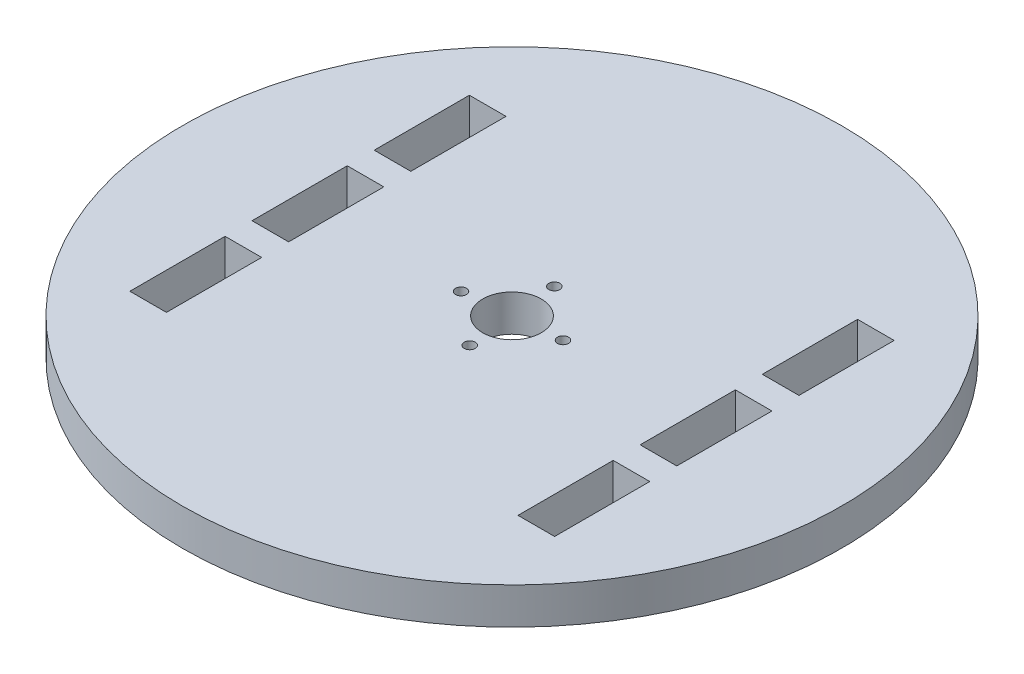
SolidWorks part; units mm, degrees
material "Acrylic (Medium-high impact)"
ref_plane "Front Plane" through (0, 0, 0) normal (0, 0, 1) x (1, 0, 0)
ref_plane "Top Plane" through (0, 0, 0) normal (0, 1, 0) x (1, 0, 0)
ref_plane "Right Plane" through (0, 0, 0) normal (1, 0, 0) x (0, 0, -1)
sketch "Sketch1" plane through (0, 0, 0) normal (0, 1, 0) x (1, 0, 0)
  line L0 (29, -23.1821) -> (29, -10.1821)
  line L1 (24, 23.1821) -> (24, 10.1821)
  line L2 (0, 45) -> (0, -45) construction
  line L4 (-29, -23.1821) -> (-24, -23.1821)
  line L5 (29, -23.1821) -> (24, -23.1821)
  line L6 (-45, 0) -> (45, 0) construction
  line L7 (29, 23.1821) -> (24, 23.1821)
  line L8 (24, 10.1821) -> (29, 10.1821)
  line L9 (24, -10.1821) -> (29, -10.1821)
  line L10 (24, 6.5) -> (29, 6.5)
  line L11 (24, -6.5) -> (29, -6.5)
  line L14 (-24, -10.1821) -> (-29, -10.1821)
  line L15 (-24, -6.5) -> (-29, -6.5)
  line L16 (-24, 6.5) -> (-29, 6.5)
  line L17 (-24, 10.1821) -> (-29, 10.1821)
  line L18 (-24, 23.1821) -> (-24, 10.1821)
  line L20 (-29, 23.1821) -> (-24, 23.1821)
  line L21 (-29, -23.1821) -> (-29, -10.1821)
  line L22 (24, 6.5) -> (24, -6.5)
  line L23 (29, 10.1821) -> (29, 23.1821)
  line L24 (24, -10.1821) -> (24, -23.1821)
  line L25 (29, -6.5) -> (29, 6.5)
  line L26 (-24, 6.5) -> (-24, -6.5)
  line L27 (-29, 10.1821) -> (-29, 23.1821)
  line L28 (-24, -10.1821) -> (-24, -23.1821)
  line L29 (-29, -6.5) -> (-29, 6.5)
  circle A0 centre (0, 0) radius 45
  circle A1 centre (0, 0) radius 4
  circle A9 centre (0, 0) radius 6.3965 construction
  circle A12 centre (6.3689, 0.5932) radius 0.75
  circle A14 centre (0.5932, -6.3689) radius 0.75
  circle A15 centre (-0.5932, 6.3689) radius 0.75
  circle A16 centre (-6.3689, -0.5932) radius 0.75
  point P16 (0, 0)
  dimension "D1" = 90
  dimension "D2" = 8
  dimension "D3" = 48
  dimension "D6" = 5
  dimension "D8" = 13
  dimension "D9" = 6.5
extrude "Boss-Extrude1" add sketch "Sketch1" along normal blind 5
